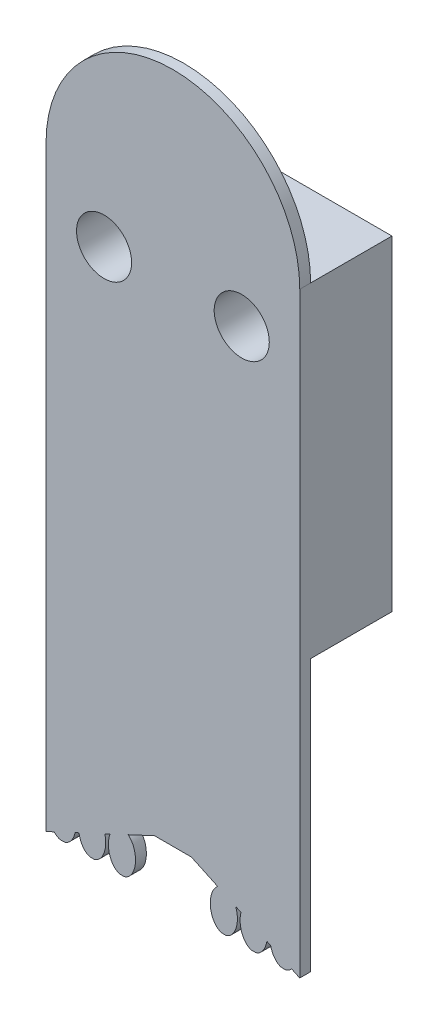
SolidWorks part; units mm, degrees
ref_plane "Front Plane" through (0, 0, 0) normal (0, 0, 1) x (1, 0, 0)
ref_plane "Top Plane" through (0, 0, 0) normal (0, 1, 0) x (1, 0, 0)
ref_plane "Right Plane" through (0, 0, 0) normal (1, 0, 0) x (0, 0, -1)
sketch "Sketch1" plane through (0, 0, 0) normal (0, 0, 1) x (1, 0, 0)
  line L0 (-211.9068, 229.6911) -> (-211.9068, -47.1689) construction
  line L1 (-169.1078, 185.3681) -> (-169.1078, -2.8459) construction
  line L2 (-135.7068, 305.8911) -> (54.7932, 305.8911) construction
  line L3 (130.9932, 229.6911) -> (130.9932, -47.1689) construction
  line L4 (54.7932, -123.3689) -> (-135.7068, -123.3689) construction
  line L5 (-117.6728, 236.8031) -> (36.6322, 236.8031) construction
  line L6 (-169.1078, 185.3681) -> (-169.1078, -2.8459) construction
  line L7 (-117.6728, -54.2809) -> (33.7008, -54.2809) construction
  line L8 (88.0672, 184.1399) -> (88.0672, -2.8459) construction
  line L9 (-117.6728, -54.2809) -> (33.7008, -54.2809) construction
  line L10 (88.0672, -2.8459) -> (88.0672, 184.1399) construction
  line L11 (36.6322, 236.8031) -> (-117.6728, 236.8031)
  line L12 (-211.9068, 229.6911) -> (-211.9068, -47.1689) construction
  line L13 (-135.7068, -123.3689) -> (54.7932, -123.3689)
  line L14 (130.9932, -47.1689) -> (130.9932, 229.6911) construction
  line L15 (54.7932, 305.8911) -> (-135.7068, 305.8911)
  line L16 (-209.0727, 380.8211) -> (155.9253, 380.8211) construction
  line L17 (230.8553, 305.8911) -> (230.8553, -298.1209) construction
  line L18 (155.9253, -373.0509) -> (-209.0727, -373.0509) construction
  line L19 (-284.0027, -298.1209) -> (-284.0027, 305.8911) construction
  line L20 (-209.0727, 360.8211) -> (155.9253, 360.8211)
  line L21 (210.8553, 305.8911) -> (210.8553, -298.1209)
  line L22 (155.9253, -353.0509) -> (-209.0727, -353.0509)
  line L23 (-264.0027, -298.1209) -> (-264.0027, 305.8911)
  line L24 (-264.0027, -143.3689) -> (210.8553, -143.3689)
  line L25 (-26.5737, -353.0509) -> (-26.5737, -143.3689) construction
  line L26 (11.5263, -314.9509) -> (11.5263, -162.5509)
  line L27 (-39.2737, -314.9509) -> (-13.8737, -314.9509)
  line L28 (-39.2737, -314.9509) -> (-39.2737, -162.5509)
  line L29 (-39.2737, -162.5509) -> (-13.8737, -162.5509)
  line L30 (-13.8737, -314.9509) -> (-13.8737, -162.5509)
  line L31 (36.9263, -276.8509) -> (36.9263, -162.5509)
  line L32 (11.5263, -314.9509) -> (24.2263, -314.9509)
  line L33 (11.5263, -162.5509) -> (36.9263, -162.5509)
  line L34 (62.3263, -276.8509) -> (62.3263, -162.5509)
  line L35 (87.7263, -314.9509) -> (87.7263, -162.5509)
  line L36 (75.0263, -314.9509) -> (87.7263, -314.9509)
  line L37 (62.3263, -162.5509) -> (87.7263, -162.5509)
  line L38 (113.1263, -314.9509) -> (113.1263, -162.5509)
  line L39 (138.5263, -299.0035) -> (138.5263, -162.5509)
  line L40 (113.1263, -314.9509) -> (114.2197, -314.9509)
  line L41 (113.1263, -162.5509) -> (138.5263, -162.5509)
  line L42 (163.9263, -277.9614) -> (163.9263, -162.5509)
  line L43 (189.3263, -250.8766) -> (189.3263, -162.5509)
  line L44 (163.9263, -162.5509) -> (189.3263, -162.5509)
  line L45 (-90.0737, -276.8509) -> (-90.0737, -162.5509)
  line L46 (-64.6737, -314.9509) -> (-64.6737, -162.5509)
  line L47 (-77.3737, -314.9509) -> (-64.6737, -314.9509)
  line L48 (-90.0737, -162.5509) -> (-64.6737, -162.5509)
  line L49 (-140.8616, -314.9509) -> (-140.8616, -162.5509)
  line L50 (-115.4616, -276.8509) -> (-115.4616, -162.5509)
  line L51 (-140.8616, -314.9509) -> (-128.1616, -314.9509)
  line L52 (-140.8616, -162.5509) -> (-115.4616, -162.5509)
  line L53 (-191.6737, -299.0035) -> (-191.6737, -162.5509)
  line L54 (-166.2737, -314.9509) -> (-166.2737, -162.5509)
  line L55 (-167.367, -314.9509) -> (-166.2737, -314.9509)
  line L56 (-191.6737, -162.5509) -> (-166.2737, -162.5509)
  line L57 (-242.4737, -250.8766) -> (-242.4737, -162.5509)
  line L58 (-217.0737, -277.9614) -> (-217.0737, -162.5509)
  line L59 (-242.4737, -162.5509) -> (-217.0737, -162.5509)
  line L60 (-264.0027, -298.1209) -> (-264.0027, -143.3689)
  line L61 (-115.4616, -276.8509) -> (-128.1616, -276.8509)
  line L62 (-128.1616, -314.9509) -> (-128.1616, -276.8509)
  line L63 (-90.0737, -276.8509) -> (-77.3737, -276.8509)
  line L64 (-77.3737, -314.9509) -> (-77.3737, -276.8509)
  line L65 (62.3263, -276.8509) -> (75.0263, -276.8509)
  line L66 (75.0263, -314.9509) -> (75.0263, -276.8509)
  line L67 (36.9263, -276.8509) -> (24.2263, -276.8509)
  line L68 (24.2263, -314.9509) -> (24.2263, -276.8509)
  line L69 (210.8553, -298.1209) -> (210.8553, -143.3689)
  line L71 (-126.1616, -283.3689) -> (-79.3737, -283.3689)
  line L72 (-126.1616, -283.3689) -> (-126.1616, -343.3689)
  line L73 (-126.1616, -343.3689) -> (-79.3737, -343.3689)
  line L74 (-79.3737, -283.3689) -> (-79.3737, -343.3689)
  arc A0 (-169.1078, -2.8459) -> (-117.6728, -54.2809) centre (-117.6728, -2.8459) ccw construction
  arc A1 (33.7008, -54.2809) -> (88.0672, -2.8459) centre (33.7008, 0.169) ccw construction
  arc A2 (88.0672, 184.1399) -> (36.6322, 236.8031) centre (35.3893, 184.1399) ccw
  arc A3 (-117.6728, 236.8031) -> (-169.1078, 185.3681) centre (-117.6728, 185.3681) ccw construction
  arc A4 (-211.9068, -47.1689) -> (-135.7068, -123.3689) centre (-135.7068, -47.1689) ccw construction
  arc A5 (54.7932, -123.3689) -> (130.9932, -47.1689) centre (54.7932, -47.1689) ccw construction
  arc A6 (130.9932, 229.6911) -> (54.7932, 305.8911) centre (54.7932, 229.6911) ccw construction
  arc A7 (-135.7068, 305.8911) -> (-211.9068, 229.6911) centre (-135.7068, 229.6911) ccw construction
  arc A8 (-284.0027, 305.8911) -> (-209.0727, 380.8211) centre (-209.0727, 305.8911) cw construction
  arc A9 (230.8553, 305.8911) -> (155.9253, 380.8211) centre (155.9253, 305.8911) ccw construction
  arc A10 (230.8553, -298.1209) -> (155.9253, -373.0509) centre (155.9253, -298.1209) cw construction
  arc A11 (-209.0727, -373.0509) -> (-284.0027, -298.1209) centre (-209.0727, -298.1209) cw construction
  arc A12 (210.8553, 305.8911) -> (155.9253, 360.8211) centre (155.9253, 305.8911) ccw
  arc A13 (210.8553, -298.1209) -> (155.9253, -353.0509) centre (155.9253, -298.1209) cw
  arc A14 (-209.0727, -353.0509) -> (-264.0027, -298.1209) centre (-209.0727, -298.1209) cw
  arc A15 (-264.0027, 305.8911) -> (-209.0727, 360.8211) centre (-209.0727, 305.8911) cw
  arc A16 (-242.4737, -250.8766) -> (-217.0737, -277.9614) centre (-26.5737, -73.8595) ccw
  arc A17 (-191.6737, -299.0035) -> (-167.367, -314.9509) centre (-26.5737, -73.8595) ccw
  arc A18 (114.2197, -314.9509) -> (138.5263, -299.0035) centre (-26.5737, -73.8595) ccw
  arc A19 (163.9263, -277.9614) -> (189.3263, -250.8766) centre (-26.5737, -73.8595) ccw
  circle A20 centre (-115.4616, -294.6309) radius 5.08
  circle A21 centre (-90.0737, -294.6309) radius 5.08
  circle A22 centre (36.9263, -294.6309) radius 5.08
  circle A23 centre (62.3263, -294.6309) radius 5.08
  point P0 (-135.7068, 305.8911)
  point P1 (54.7932, 305.8911)
  point P2 (130.9932, 229.6911)
  point P3 (130.9932, -47.1689)
  point P4 (-117.6728, 236.8031)
  point P5 (36.6322, 236.8031)
  point P7 (88.0672, 184.1399)
  point P8 (88.0672, -2.8459)
  point P9 (36.6322, -54.2809)
  point P10 (-117.6728, -54.2809)
  point P11 (-169.1078, -2.8459)
  point P12 (-169.1078, 185.3681)
  point P13 (54.7932, -123.3689)
  point P14 (-135.7068, -123.3689)
  point P26 (-211.9068, -47.1689)
  point P28 (-211.9068, 229.6911)
  point P73 (-26.5737, -314.9509)
  point P74 (-26.5737, -162.5509)
  point P75 (-26.5737, -162.5509)
  point P80 (-264.0027, -220.7449)
  point P81 (210.8553, -220.7449)
  dimension "D28" = 10.16
  dimension "D29" = 10.16
  dimension "D30" = 10.16
  dimension "D31" = 10.16
  dimension "D1" = 20
  dimension "D2" = 25.4
  dimension "D3" = 152.4
  dimension "D4" = 38.1
  dimension "D5" = 237.429
  dimension "D6" = 12.7
  dimension "D7" = 12.7
  dimension "D8" = 38.1
  dimension "D9" = 38.1
  dimension "D10" = 12.7
  dimension "D11" = 12.7
  dimension "D12" = 38.1
  dimension "D13" = 38.1
  dimension "D14" = 12.7
  dimension "D15" = 12.7
  dimension "D16" = 12.7
  dimension "D17" = 17.78
  dimension "D18" = 17.78
  dimension "D19" = 12.7
  dimension "D20" = 17.78
  dimension "D21" = 17.78
  dimension "D22" = 60
  dimension "D23" = 140
  dimension "D24" = 2
  dimension "D25" = 2
  dimension "D26" = 50.8
  dimension "D27" = 101.5879
extrude "Boss-Extrude1" add sketch "Sketch1" along normal blind 15 contours L74 L71 L72 L73 A21 A20
sketch "Sketch2" plane through (0, 0, 15) normal (0, 0, 1) x (1, 0, 0)
  line L0 (-126.1616, -283.3689) -> (-79.3737, -283.3689) construction
  line L1 (-126.1616, -393.3689) -> (-124.6549, -392.6663)
  line L2 (-126.1616, -283.3689) -> (-79.3737, -283.3689)
  line L3 (-126.1616, -283.3689) -> (-126.1616, -393.3689)
  line L4 (-126.1616, -393.3689) -> (-79.3737, -393.3689)
  line L5 (-79.3737, -283.3689) -> (-79.3737, -393.3689)
  line L6 (-79.3737, -393.3689) -> (-80.8803, -392.6663)
  line L7 (-106.1616, -384.0428) -> (-99.3737, -384.0428)
  line L8 (-102.7676, -393.3689) -> (-102.7676, -343.3689) construction
  line L9 (-126.1616, -343.3689) -> (-79.3737, -343.3689) construction
  line L10 (-111.0317, -386.3137) -> (-106.1616, -384.0428)
  line L11 (-115.3272, -388.3167) -> (-114.3567, -387.8642)
  line L12 (-120.7947, -390.8663) -> (-120.0918, -390.5385)
  line L13 (-94.5036, -386.3137) -> (-99.3737, -384.0428)
  line L14 (-90.2081, -388.3167) -> (-91.1785, -387.8642)
  line L15 (-84.7405, -390.8663) -> (-85.4434, -390.5385)
  arc A0 (-79.3737, -283.3689) -> (-126.1616, -283.3689) centre (-102.7676, -283.3689) ccw
  ellipse E0 centre (-123.1616, -389.6588) end of major axis (-123.1616, -385.9088) minor radius 2.5 (-124.6549, -392.6663) -> (-120.7947, -390.8663) ccw
  ellipse E1 centre (-117.6616, -389.6588) end of major axis (-117.6616, -385.9088) minor radius 2.5 (-120.0918, -390.5385) -> (-115.3272, -388.3167) ccw
  ellipse E2 centre (-112.1616, -389.6588) end of major axis (-112.1616, -385.9088) minor radius 2.5 (-114.3567, -387.8642) -> (-111.0317, -386.3137) ccw
  ellipse E3 centre (-93.3737, -389.6588) end of major axis (-93.3737, -385.9088) minor radius 2.5 (-91.1785, -387.8642) -> (-94.5036, -386.3137) cw
  ellipse E4 centre (-87.8737, -389.6588) end of major axis (-87.8737, -385.9088) minor radius 2.5 (-85.4434, -390.5385) -> (-90.2081, -388.3167) cw
  ellipse E5 centre (-82.3737, -389.6588) end of major axis (-82.3737, -385.9088) minor radius 2.5 (-80.8803, -392.6663) -> (-84.7405, -390.8663) cw
  circle M11 centre (-90.0737, -294.6309) radius 5.08
  circle M12 centre (-115.4616, -294.6309) radius 5.08
  line M13 (-79.3737, -343.3689) -> (-79.3737, -283.3689)
  line M14 (-79.3737, -283.3689) -> (-126.1616, -283.3689)
  line M15 (-126.1616, -283.3689) -> (-126.1616, -343.3689)
  line M16 (-126.1616, -343.3689) -> (-79.3737, -343.3689)
  dimension "D1" = 110
  dimension "D2" = 25
  dimension "D3" = 20
  dimension "D4" = 25
  dimension "D5" = 20
  dimension "D6" = 7.5
  dimension "D7" = 5
  dimension "D8" = 3
  dimension "D9" = 3
extrude "Boss-Extrude2" add sketch "Sketch2" along normal blind 2 contours L8 L7 L13 E3 L4 L14 E4 L15 E5 L6 L5 M16 | L7 L8 L3 L1 E0 L4 L12 E1 L11 E2 L10 M16 | M16 M13 M14 M15 M12 M11 | A0 M14
